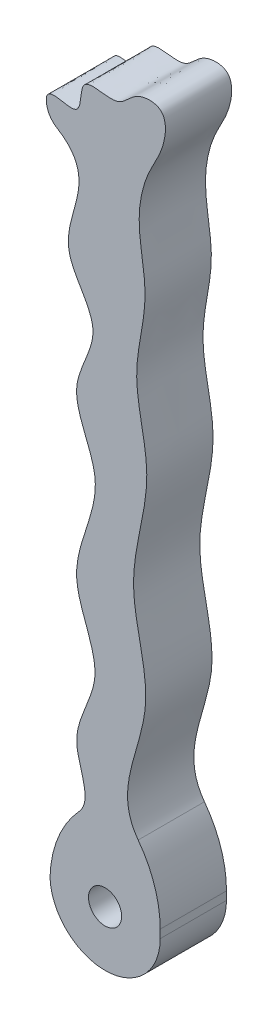
SolidWorks part; units mm, degrees
ref_plane "Front Plane" through (0, 0, 0) normal (0, 0, 1) x (1, 0, 0)
ref_plane "Top Plane" through (0, 0, 0) normal (0, 1, 0) x (1, 0, 0)
ref_plane "Right Plane" through (0, 0, 0) normal (1, 0, 0) x (0, 0, -1)
sketch "Sketch1" plane through (0, 0, 0) normal (0, 0, 1) x (1, 0, 0)
  line L0 (4.99, 0) -> (4.99, -9.98) construction
  line L2 (0, 0) -> (0, -9.98)
  line L3 (0, -9.98) -> (9.98, -9.98)
  line L4 (9.98, 0) -> (9.98, -9.98)
  circle A0 centre (4.99, -4.99) radius 1.5
  spline S0 degree 3 poles (0, 54.2507) (-1.3002, 57.7322) (3.2647, 54.3642) (2.4263, 59.6713) (6.2497, 57.9313) (7.56, 60.3083) (10.809, 60.4277) (10.3371, 56.9019) (8.6679, 54.3949) (7.6248, 50.0404) (9.268, 44.5549) (7.0461, 37.9736) (9.8469, 30.217) (6.2703, 21.6733) (10.7937, 11.1069) (4.4749, 3.4165) (9.98, 0) knots 0 0 0 0 0.053422 0.084053 0.123826 0.153488 0.181182 0.220513 0.254556 0.310198 0.388256 0.476668 0.57334 0.700293 0.819187 1 1 1 1
  spline S1 degree 3 poles (0, 54.2507) (5.0844, 51.6989) (-1.0405, 45.9919) (5.4473, 39.8872) (0.9091, 34.169) (6.0054, 27.5034) (0.487, 20.0549) (5.6717, 12.8445) (0.4035, 6.2112) (5.1771, 1.3503) (0, 0) knots 0 0 0 0 0.175025 0.26981 0.365352 0.476782 0.633954 0.755983 0.862891 1 1 1 1
  dimension "D3" = 3
  dimension "D1" = 9.98
  dimension "D2" = 9.98
extrude "Boss-Extrude1" add sketch "Sketch1" along normal blind 6
fillet "Fillet1" radius 10 2 edges at (9.98, 0, 3) (0, 0, 3)
fillet "Fillet2" radius 2 1 edges at (0, 54.2507, 3)
sketch "Sketch2" plane through (0, 0, 6) normal (0, 0, 1) x (1, 0, 0)
  line L1 (-3.1937, -4.99) -> (16.0799, -4.99)
  line L2 (-3.1937, -4.99) -> (-3.1937, -13.2025)
  line L3 (-3.1937, -13.2025) -> (16.0799, -13.2025)
  line L4 (16.0799, -4.99) -> (16.0799, -13.2025)
  circle A0 centre (4.99, -4.99) radius 4.99
  arc M4 (2.6271, 1.3052) -> (0, -5.4506) centre (10, -5.4506) ccw
  line M5 (0, -5.4506) -> (0, -9.98)
  line M6 (0, -9.98) -> (9.98, -9.98)
  line M7 (9.98, -9.98) -> (9.98, -4.2439)
extrude "Cut-Extrude1" cut sketch "Sketch2" against normal blind 6 contours A0 M4 M5 M6 | A0 M6 M7
